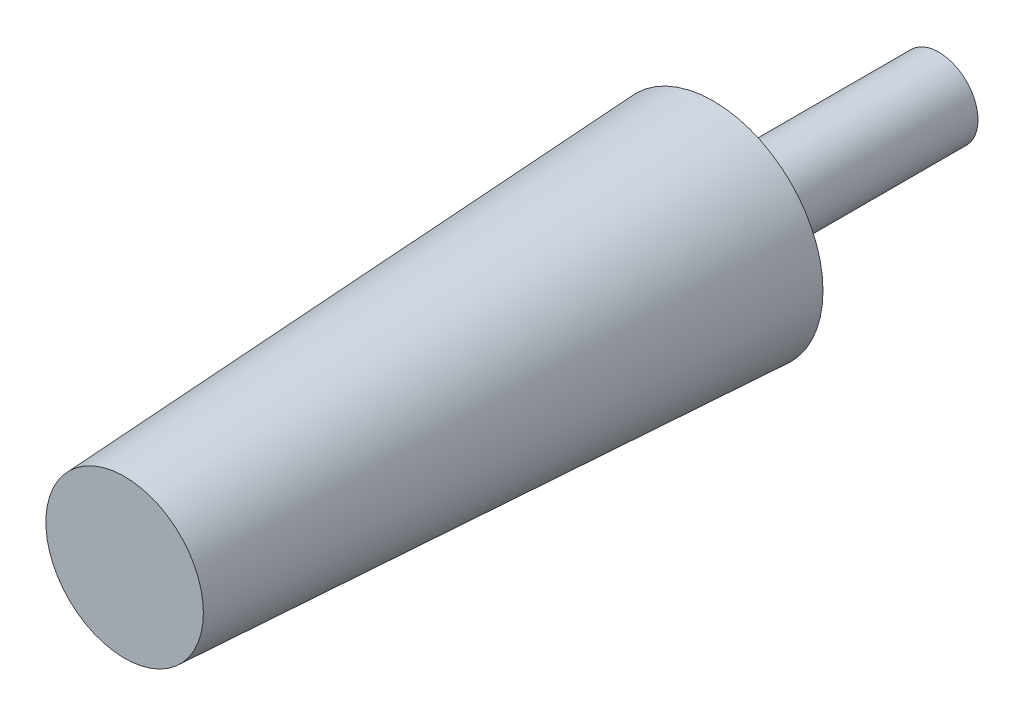
SolidWorks part; units mm, degrees
ref_plane "Front Plane" through (0, 0, 0) normal (0, 0, 1) x (1, 0, 0)
ref_plane "Top Plane" through (0, 0, 0) normal (0, 1, 0) x (1, 0, 0)
ref_plane "Right Plane" through (0, 0, 0) normal (1, 0, 0) x (0, 0, -1)
sketch "Sketch3" plane through (0, 0, 0) normal (0, 0, 1) x (1, 0, 0)
  circle A0 centre (0, 0) radius 3.9688
  dimension "D1" = 7.9375
extrude "Boss-Extrude1" add sketch "Sketch3" along normal blind 22.86
sketch "Sketch4" plane through (0, 0, 22.86) normal (0, 0, 1) x (1, 0, 0)
  circle A0 centre (0, 0) radius 11.1125
  dimension "D1" = 22.225
extrude "Boss-Extrude2" add sketch "Sketch4" along normal blind 59.69 draft 3
